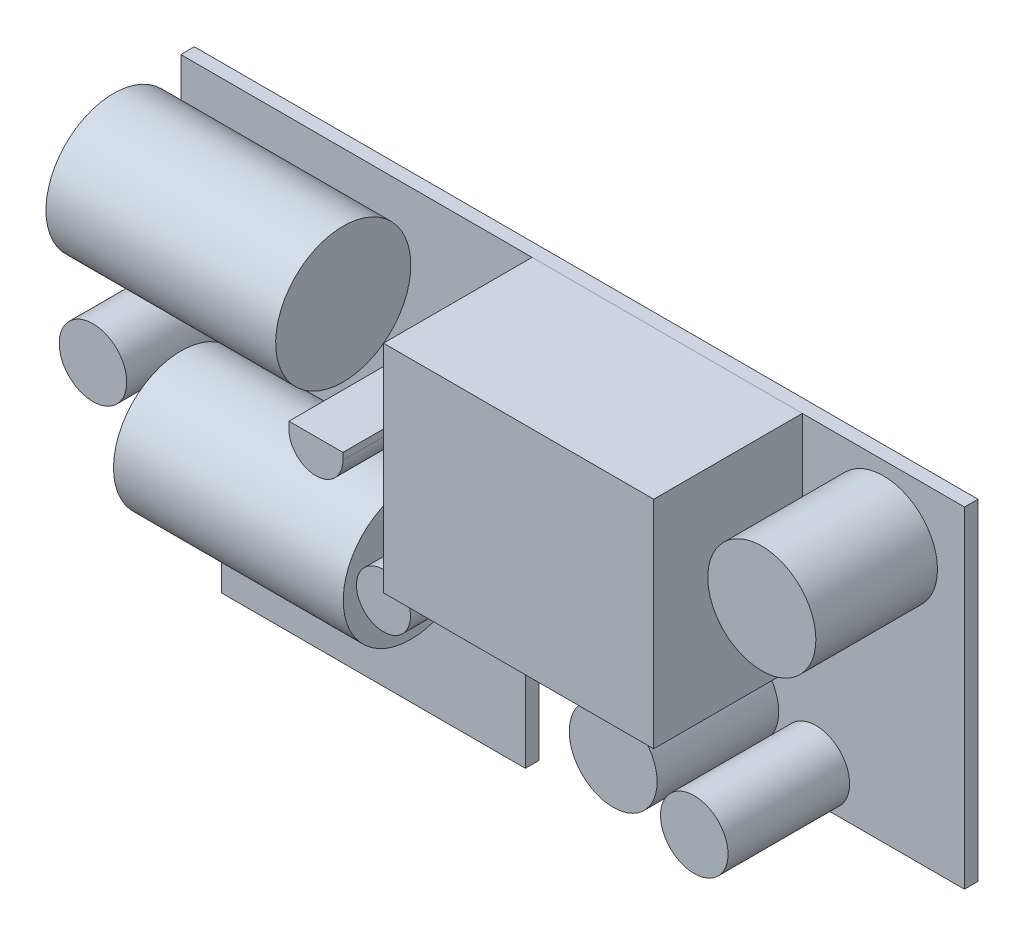
SolidWorks part; units mm, degrees
material "AISI 1020"
ref_plane "Plano superior" through (0, 0, 0) normal (0, 0, 1) x (1, 0, 0)
ref_plane "Plano frontal" through (0, 0, 0) normal (0, 1, 0) x (1, 0, 0)
ref_plane "Plano direito" through (0, 0, 0) normal (1, 0, 0) x (0, 0, -1)
sketch "Esboço1" plane through (0, 0, 0) normal (0, 0, 1) x (1, 0, 0)
  line L1 (-29, 16.5) -> (29, 16.5)
  line L2 (-29, 16.5) -> (-29, -16.5)
  line L3 (-29, -16.5) -> (29, -16.5)
  line L4 (29, 16.5) -> (29, -16.5)
  line L5 (-29, 16.5) -> (29, -16.5) construction
  line L6 (-29, -16.5) -> (29, 16.5) construction
  point P0 (0, 0)
  dimension "D1" = 33
  dimension "D2" = 58
extrude "Ressalto-extrusão1" add sketch "Esboço1" along normal blind 1
sketch "Esboço2" plane through (0, 0, 1) normal (0, 0, 1) x (1, 0, 0)
  line L0 (-29, -16.5) -> (29, -16.5) construction
  line L1 (-29, -16.5) -> (-26, -16.5)
  line L2 (-29, -16.5) -> (-29, -8)
  line L3 (-29, -8) -> (-26, -8)
  line L4 (-26, -16.5) -> (-26, -8)
  line L5 (-3.5, -16.5) -> (29, -16.5)
  line L6 (-3.5, -16.5) -> (-3.5, -8)
  line L7 (-3.5, -8) -> (29, -8)
  line L8 (29, -16.5) -> (29, -8)
  line L9 (29, -16.5) -> (29, 16.5) construction
  dimension "D1" = 8.5
  dimension "D2" = 3
  dimension "D3" = 22.5
extrude "Corte-extrusão1" cut sketch "Esboço2" against normal through all
sketch "Esboço3" plane through (0, 0, 1) normal (0, 0, 1) x (1, 0, 0)
  line L0 (29, 16.5) -> (-29, 16.5) construction
  line L1 (-3, 16.5) -> (17, 16.5)
  line L2 (-3, 16.5) -> (-3, 0.5)
  line L3 (-3, 0.5) -> (17, 0.5)
  line L4 (17, 16.5) -> (17, 0.5)
  line L5 (-29, 16.5) -> (-29, -8) construction
  dimension "D1" = 26
  dimension "D2" = 20
  dimension "D3" = 16
extrude "Ressalto-extrusão2" add sketch "Esboço3" along normal blind 11 separate body
sketch "Esboço4" plane through (0, 0, 1) normal (0, 0, 1) x (1, 0, 0)
  line L0 (-3, 16.5) -> (-3, 0.5) construction
  line L1 (29, 16.5) -> (-29, 16.5) construction
  line L2 (-26, -16.5) -> (-3.5, -16.5) construction
  line L5 (-29, 16.5) -> (-29, -8) construction
  line L6 (29, -8) -> (29, 16.5) construction
  line L7 (29, -8) -> (-3.5, -8) construction
  line L9 (-12, 6) -> (-8, 6)
  line L10 (-12, 6) -> (-12, 5.5)
  line L11 (-12, 5.5) -> (-8, 5.5) construction
  line L12 (-8, 6) -> (-8, 5.5)
  circle A0 centre (12, -3.5) radius 3.25
  circle A1 centre (18, -5.5) radius 2.5
  circle A2 centre (23, 11.5) radius 4
  circle A5 centre (-26.5, 2.5) radius 2.5
  circle A6 centre (-5, -2) radius 2
  arc A7 (-12, 5.5) -> (-8, 5.5) centre (-10, 5.5) ccw
  dimension "D1" = 6.5
  dimension "D4" = 5
  dimension "D5" = 8
  dimension "D7" = 5
  dimension "D8" = 14
  dimension "D9" = 4
  dimension "D10" = 14.5
  dimension "D12" = 11
  dimension "D14" = 0.5
  dimension "D16" = 2
  dimension "D17" = 19
  dimension "D2" = 15
  dimension "D3" = 20
  dimension "D6" = 26
  dimension "D11" = 24
  dimension "D13" = 4
  dimension "D15" = 11
extrude "Ressalto-extrusão3" add sketch "Esboço4" along normal blind 9 separate body
sketch "Esboço5" plane through (-29, 0, 0) normal (-1, 0, 0) x (0, 0, 1)
  line L0 (1, 16.5) -> (0, 16.5) construction
  circle A0 centre (5.9787, 11.5) radius 5
  dimension "D1" = 10
extrude "Ressalto-extrusão4" add sketch "Esboço5" against normal blind 17 separate body
sketch "Esboço6" plane through (-29, 0, 0) normal (-1, 0, 0) x (0, 0, 1)
  line L0 (5.9787, 11.5) -> (5.9787, -2.5) construction
  circle A0 centre (5.9787, -2.5) radius 5
  circle A1 centre (5.9787, 11.5) radius 5 construction
  point P5 (5.9787, -4)
  point P9 (5.9787, -4)
  dimension "D1" = 14
extrude "Ressalto-extrusão5" add sketch "Esboço6" against normal blind 17 from offset 5 separate body offset against normal yes
